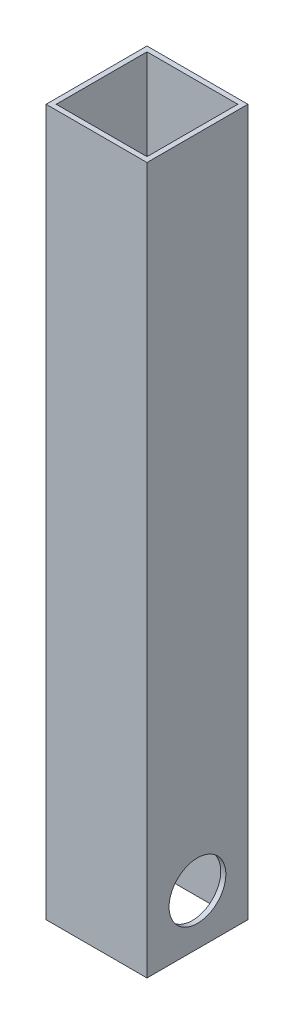
SolidWorks part; units mm, degrees
ref_plane "Front Plane" through (0, 0, 0) normal (0, 0, 1) x (1, 0, 0)
ref_plane "Top Plane" through (0, 0, 0) normal (0, 1, 0) x (1, 0, 0)
ref_plane "Right Plane" through (0, 0, 0) normal (1, 0, 0) x (0, 0, -1)
sketch "Sketch1" plane through (0, 0, 0) normal (0, 1, 0) x (1, 0, 0)
  line L0 (2.54, -2.54) -> (48.26, -2.54)
  line L1 (0, 0) -> (50.8, 0)
  line L2 (0, 0) -> (0, -50.8)
  line L3 (0, -50.8) -> (50.8, -50.8)
  line L4 (50.8, 0) -> (50.8, -50.8)
  line L5 (48.26, -2.54) -> (48.26, -48.26)
  line L6 (2.54, -48.26) -> (48.26, -48.26)
  line L7 (2.54, -2.54) -> (2.54, -48.26)
  dimension "D1" = 50.8
  dimension "D2" = 50.8
  dimension "D3" = 2.54
extrude "Boss-Extrude1" add sketch "Sketch1" along normal blind 355.6
sketch "Sketch2" plane through (0, 0, 0) normal (-1, 0, 0) x (0, 0, 1)
  line L0 (0, 0) -> (50.8, 0) construction
  line L1 (0, 0) -> (50.8, 0) construction
  circle A0 centre (25.4, 25.4) radius 14.2875
  point P4 (0, 0)
  point P5 (0, 0)
  point P6 (23.978, 25.4)
  point P7 (25.4, 0)
  dimension "D1" = 28.575
  dimension "D2" = 25.4
extrude "Cut-Extrude1" cut sketch "Sketch2" against normal up to surface (50.8 mm away) contours A0 up to face at (50.8, 177.8, 25.4)
